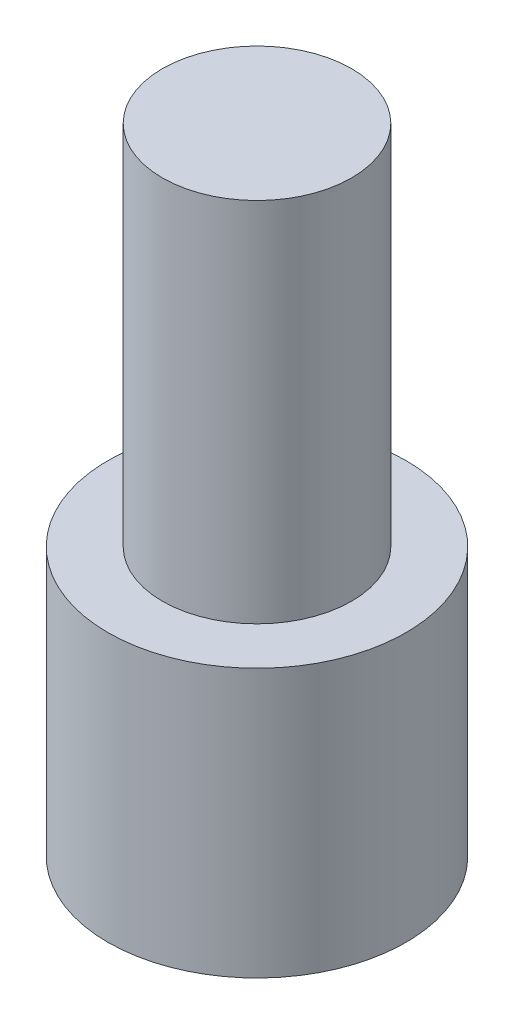
SolidWorks part; units mm, degrees
ref_plane "Спереди" through (0, 0, 0) normal (0, 0, 1) x (1, 0, 0)
ref_plane "Сверху" through (0, 0, 0) normal (0, 1, 0) x (1, 0, 0)
ref_plane "Справа" through (0, 0, 0) normal (1, 0, 0) x (0, 0, -1)
sketch "Эскиз1" plane through (0, 0, 0) normal (0, 1, 0) x (1, 0, 0)
  circle A0 centre (0, 0) radius 5
  dimension "D1" = 10
extrude "Бобышка-Вытянуть1" add sketch "Эскиз1" along normal blind 9
sketch "Эскиз2" plane through (0, 9, 0) normal (0, 1, 0) x (1, 0, 0)
  circle A0 centre (0, 0) radius 3.175
  dimension "D1" = 6.35
extrude "Бобышка-Вытянуть2" add sketch "Эскиз2" along normal blind 12.3
